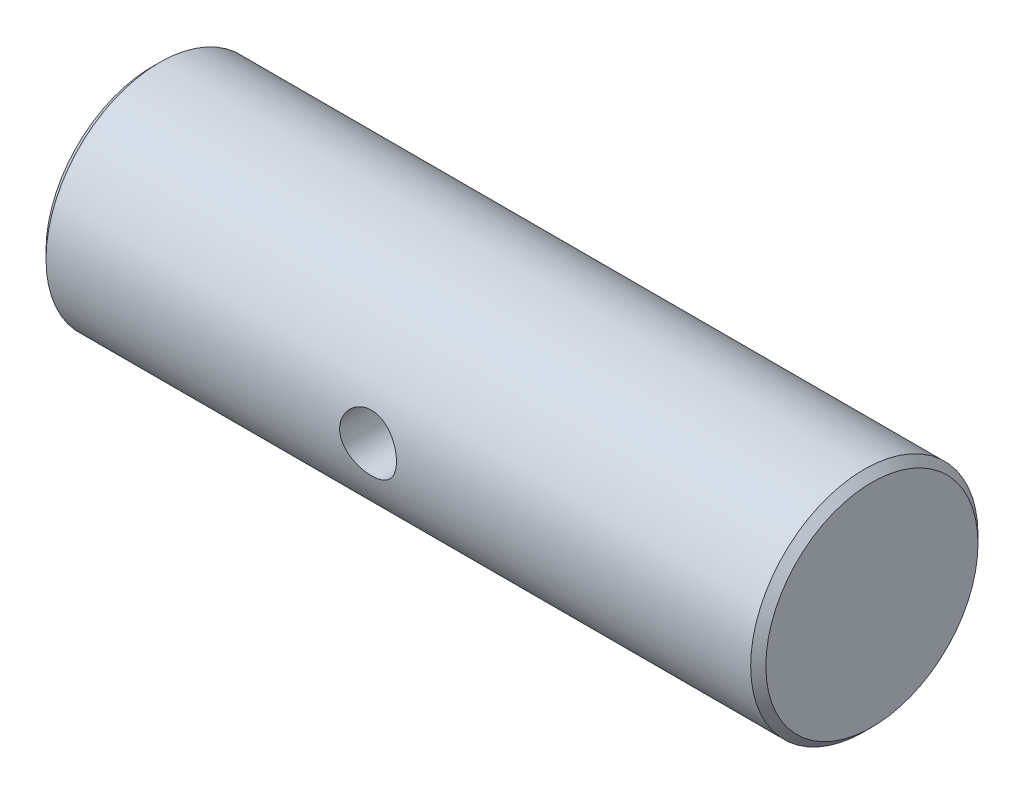
SolidWorks part; units mm, degrees
ref_plane "Plan de face" through (0, 0, 0) normal (0, 0, 1) x (1, 0, 0)
ref_plane "Plan de dessus" through (0, 0, 0) normal (0, 1, 0) x (1, 0, 0)
ref_plane "Plan de droite" through (0, 0, 0) normal (1, 0, 0) x (0, 0, -1)
sketch "Esquisse1" plane through (0, 0, 0) normal (0, 0, 1) x (1, 0, 0)
  line L1 (-15, 3) -> (4, 3)
  line L2 (-15, 3) -> (-15, 0)
  line L3 (-15, 0) -> (4, 0)
  line L4 (4, 3) -> (4, 0)
  dimension "D1" = 19
  dimension "D2" = 3
revolve "Révolution1" add sketch "Esquisse1" angle 360 about L3
chamfer "Chanfrein1" distance 0.2 angle 45 2 edges at (4, 0, 3) (-15, 0, 3)
sketch "Esquisse2" plane through (0, 0, 0) normal (0, 0, 1) x (1, 0, 0)
  line L0 (-15, 2.8) -> (-15, -2.8) construction
  circle A0 centre (-6.3, 0) radius 0.75
  dimension "D2" = 1.5
  dimension "D1" = 8.7
extrude "Enlèv. mat.-Extru.1" cut sketch "Esquisse2" against normal through all and the other way through all
